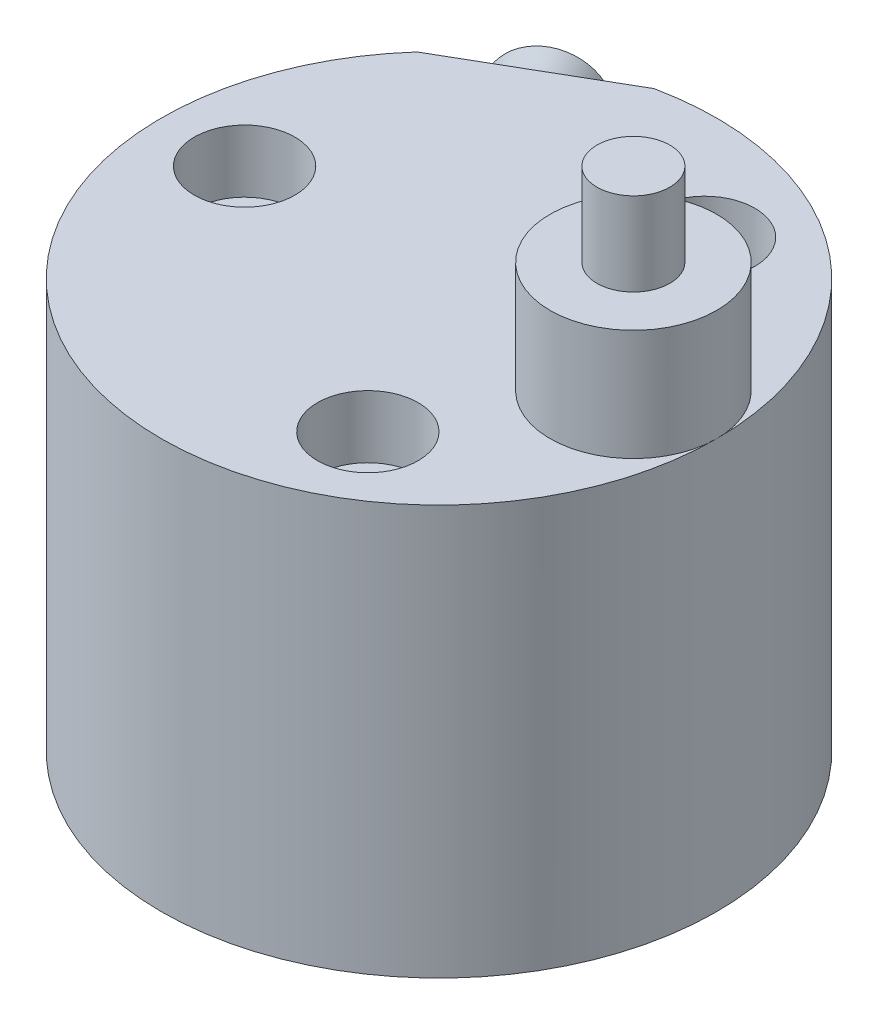
SolidWorks part; units mm, degrees
material "Alloy Steel"
ref_plane "Front Plane" through (0, 0, 0) normal (0, 0, 1) x (1, 0, 0)
ref_plane "Top Plane" through (0, 0, 0) normal (0, 1, 0) x (1, 0, 0)
ref_plane "Right Plane" through (0, 0, 0) normal (1, 0, 0) x (0, 0, -1)
sketch "Sketch1" plane through (0, 0, 0) normal (0, 1, 0) x (1, 0, 0)
  line L1 (0, 0) -> (70.7148, 0) construction
  circle A0 centre (0, 0) radius 40
  dimension "D1" = 80
extrude "Extrude1" add sketch "Sketch1" along normal blind 59
sketch "Sketch11" plane through (0, 59, 0) normal (0, 1, 0) x (1, 0, 0)
  circle A0 centre (28, 0) radius 12
  circle A1 centre (0, 0) radius 28 construction
  dimension "D1" = 24
  dimension "D2" = 56
extrude "Extrude2" add sketch "Sketch11" along normal offset from surface (16 mm away) 75 up to face at (0, 0, 40)
sketch "Sketch12" plane through (0, 75, 0) normal (0, 1, 0) x (1, 0, 0)
  circle A0 centre (28, 0) radius 5.25
  circle A1 centre (28, 0) radius 12 construction
  dimension "D1" = 10.5
extrude "Extrude3" add sketch "Sketch12" along normal blind 12
hole_wizard "Hole1" positions "Sketch4" profile "Sketch3" legacy end condition up to next
sketch "Sketch4" plane through (0, 59, 0) normal (0, 1, 0) x (-1, 0, 0)
  line L1 (0, 0) -> (54.5757, 0) construction
  circle A0 centre (0, 0) radius 28 construction
  point P7 (28, 0)
  dimension "D1" = 56
sketch "Sketch3" plane through (-28, 59, 0) normal (1, 0, 0) x (0, 0, 1)
  line L0 (0, 0) -> (0, 59.001)
  line L1 (0, 59.001) -> (4.5, 59.001)
  line L2 (4.5, 59.001) -> (4.5, 9)
  line L3 (4.5, 9) -> (7.25, 9)
  line L4 (7.25, 9) -> (7.25, 0)
  line L5 (7.25, 0) -> (0, 0)
  line L6 (0, 110) -> (0, -10) construction
  dimension "Diameter" = 9
  dimension "Depth" = 59.001
  dimension "C-Bore Diameter" = 14.5
  dimension "C-Bore Depth" = 9
pattern_circular "CirPattern1" count 3 over 360 about axis through (0, 0, 0) along (0, 1, 0) of "Hole1"
sketch "Sketch5" plane through (0, 0, 0) normal (0, -1, 0) x (1, 0, 0)
  circle A0 centre (0, 0) radius 4
  dimension "D1" = 8
extrude "Cut-Extrude1" cut sketch "Sketch5" against normal blind 4
sketch "Sketch13" plane through (0, 0, 0) normal (0, -1, 0) x (1, 0, 0)
  circle A0 centre (-14, 24.2487) radius 4
  dimension "D3" = 8
  dimension "D1" = 14
  dimension "D2" = 28
extrude "Cut-Extrude5" cut sketch "Sketch13" against normal blind 10
sketch "Sketch6" plane through (0, 0, 0) normal (0, -1, 0) x (1, 0, 0)
  line L0 (-14, -24.2487) -> (0, 0) construction
  line L1 (0, 0.0134) -> (0, -33.0799) construction
  circle A0 centre (-14, -24.2487) radius 5
  dimension "D3" = 10
  dimension "D1" = 28
  dimension "D2" = 30
extrude "Cut-Extrude2" cut sketch "Sketch6" against normal blind 3
sketch "Sketch7" plane through (0, 3, 0) normal (0, -1, 0) x (1, 0, 0)
  circle A0 centre (-14, -24.2487) radius 2
  dimension "D1" = 4
extrude "Cut-Extrude3" cut sketch "Sketch7" against normal blind 48.5
ref_plane "Plane1" through (0, 0, 0) normal (0.866, 0, -0.5) x (-0.5, 0, -0.866)
sketch "Sketch14" plane through (0, 59, 0) normal (0, 1, 0) x (1, 0, 0)
  line L0 (-29.8167, 26.664) -> (-8.1833, 39.154)
  line L1 (30.0526, -52.0526) -> (-30.0526, 52.0526) construction
  circle A0 centre (0, 0) radius 40 construction
  arc A1 (-8.1833, 39.154) -> (-29.8167, 26.664) centre (0, 0) ccw
  dimension "D1" = 38
extrude "Cut-Extrude6" cut sketch "Sketch14" against normal blind 15.5
sketch "Sketch8" plane through (0, 0, 0) normal (0.866, 0, -0.5) x (-0.5, 0, -0.866)
  line L0 (51.5856, 51.5) -> (-19.0781, 51.5) construction
  line L2 (38, 43.5) -> (38, 59) construction
  line L4 (38, 47.217) -> (38, 51.5)
  line L6 (38, 47.217) -> (23, 47.217)
  line L7 (23, 47.217) -> (23, 51.5)
  line L8 (23, 51.5) -> (38, 51.5)
  line L10 (-40, 0) -> (40, 0) construction
  dimension "D1" = 51.5
  dimension "D2" = 15
  dimension "D4" = 8.566
revolve "Cut-Revolve1" cut sketch "Sketch8" angle 360 about L0
sketch "Sketch9" plane through (0, 0, 0) normal (0.866, 0, -0.5) x (-0.5, 0, -0.866)
  line L0 (46.5879, 51.5) -> (15.4121, 51.5) construction
  line L1 (23, 51.5) -> (38, 51.5) construction
  line L4 (38, 44.5) -> (38, 47.217)
  line L5 (31.419, 47.217) -> (38, 47.217)
  line L6 (38, 44.5) -> (43, 44.5)
  line L7 (43, 44.5) -> (43, 51.5)
  line L8 (43, 51.5) -> (31, 51.5)
  line L9 (31, 51.5) -> (31, 47.636)
  line L10 (31, 47.636) -> (31.419, 47.217)
  line L13 (38, 43.5) -> (38, 59) construction
  line L14 (23, 47.217) -> (26, 47.217) construction
  dimension "D1" = 45
  dimension "D2" = 3.864
  dimension "D3" = 7
  dimension "D4" = 5
  dimension "D5" = 14
revolve "Revolve2" add sketch "Sketch9" angle 360 about L0
sketch "Sketch10" plane through (-21.5, 0, -37.2391) normal (-0.5, 0, -0.866) x (-0.866, 0, 0.5)
  line L1 (2.8868, 51.5) -> (1.4434, 54)
  line L2 (1.4434, 54) -> (-1.4434, 54)
  line L3 (-1.4434, 54) -> (-2.8868, 51.5)
  line L4 (-2.8868, 51.5) -> (-1.4434, 49)
  line L5 (-1.4434, 49) -> (1.4434, 49)
  line L6 (1.4434, 49) -> (2.8868, 51.5)
  circle A0 centre (0, 51.5) radius 2.5 construction
  circle A1 centre (0, 51.5) radius 7 construction
  dimension "D1" = 5
extrude "Cut-Extrude4" cut sketch "Sketch10" against normal blind 5
